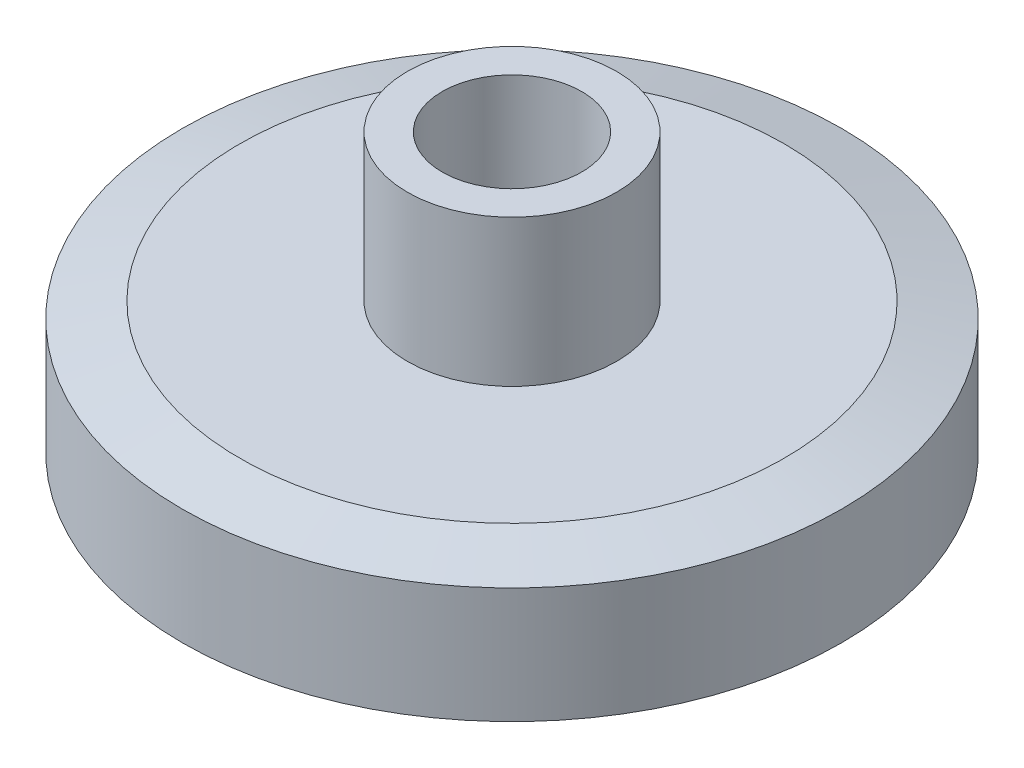
SolidWorks part; units mm, degrees
material "Сталь ШХ15 ГОСТ 801-78"
ref_plane "Plane1" through (0, 0, 0) normal (0, 0, 1) x (1, 0, 0)
ref_plane "Plane2" through (0, 0, 0) normal (0, 1, 0) x (1, 0, 0)
ref_plane "Plane3" through (0, 0, 0) normal (1, 0, 0) x (0, 0, -1)
sketch "Эскиз2" plane through (0, 0, 0) normal (0, 0, 1) x (1, 0, 0)
  line L0 (0, 0) -> (9.45, 0)
  line L1 (9.45, 0) -> (9.45, 4.2)
  line L2 (9.45, 4.2) -> (3, 4.2)
  line L3 (3, 4.2) -> (3, 8.4)
  line L4 (3, 8.4) -> (0, 8.4)
  line L5 (0, 8.4) -> (0, 0)
  dimension "D1" = 9.45
  dimension "D2" = 4.2
  dimension "3.6" = 4.2
  dimension "D4" = 3
ref_axis "Ось1" through (0, 8.4, 0) along (0, -1, 0)
revolve "Повернуть2" add sketch "Эскиз2" angle 360 about axis through (0, 8.4, 0) along (0, -1, 0)
chamfer "Фаска2" distance 1.645 angle 15 1 edges at (0, 4.2, 9.45)
chamfer "Фаска3" distance 1.645 angle 15 1 edges at (0, 0, 9.45)
sketch "Эскиз4" plane through (0, 8.4, 0) normal (0, 1, 0) x (1, 0, 0)
  circle A0 centre (0, 0) radius 2
  dimension "D1" = 4
extrude "Вырез-Вытянуть2" cut sketch "Эскиз4" against normal through all both contours A0
